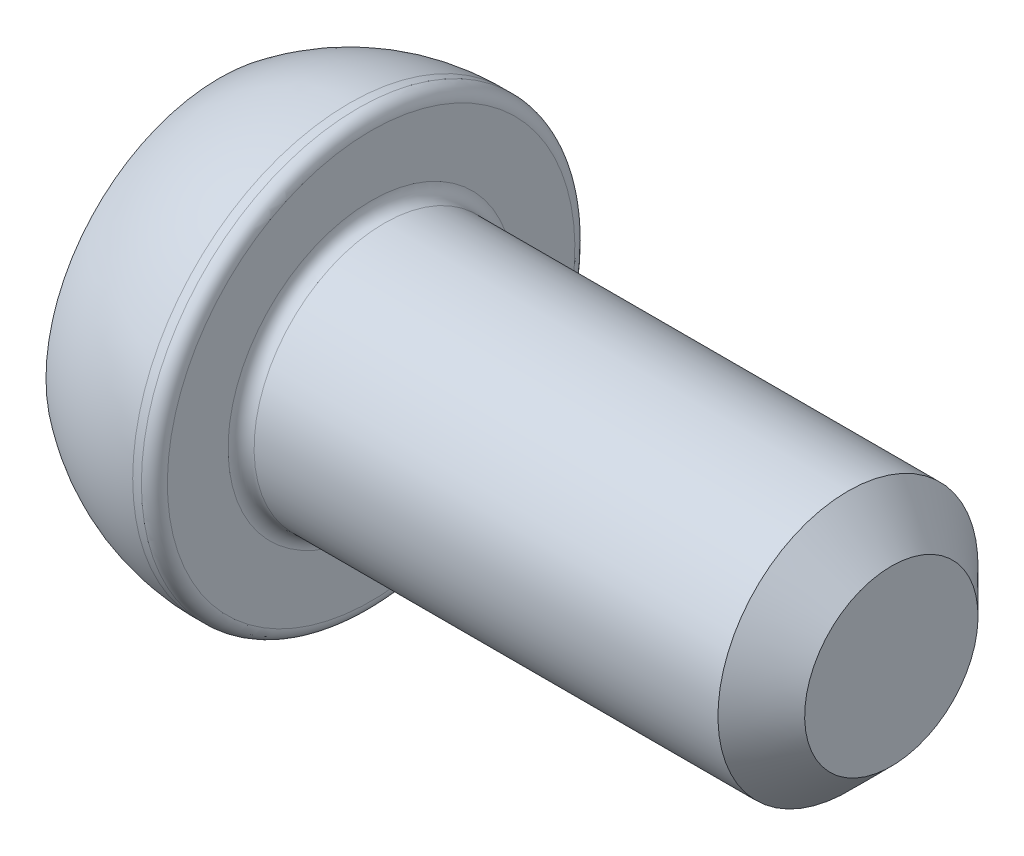
SolidWorks part; units mm, degrees
ref_plane "Спереди" through (0, 0, 0) normal (0, 0, 1) x (1, 0, 0)
ref_plane "Сверху" through (0, 0, 0) normal (0, 1, 0) x (1, 0, 0)
ref_plane "Справа" through (0, 0, 0) normal (1, 0, 0) x (0, 0, -1)
sketch "Эскиз1" plane through (0, 0, 0) normal (0, 0, 1) x (1, 0, 0)
  line L0 (0, 0) -> (0, 4)
  line L1 (3, 5) -> (3.5, 5)
  line L2 (3.5, 5) -> (3.5, 3)
  line L3 (3.5, 3) -> (15.5, 3)
  line L4 (15.5, 3) -> (15.5, 0)
  line L5 (15.5, 0) -> (0, 0) construction
  line L6 (0, 0) -> (15.5, 0)
  arc A0 (0, 4) -> (3, 5) centre (3, 0) cw
  point P9 (3.5, 4)
  dimension "D1" = 0.5
  dimension "D2" = 6
  dimension "D3" = 10
  dimension "D5" = 3.5
  dimension "D6" = 12
revolve "Повернуть1" add sketch "Эскиз1" angle 360 about L5
cosmetic thread "Условное изображение резьбы1" parameters "D2"=4.891
sketch "Эскиз2" plane through (0, 0, 0) normal (-1, 0, 0) x (0, 0, 1)
  line L1 (1.1547, 2) -> (-1.1547, 2)
  line L2 (-1.1547, 2) -> (-2.3094, 0)
  line L3 (-2.3094, 0) -> (-1.1547, -2)
  line L4 (-1.1547, -2) -> (1.1547, -2)
  line L5 (1.1547, -2) -> (2.3094, 0)
  line L6 (2.3094, 0) -> (1.1547, 2)
  circle A0 centre (0, 0) radius 2 construction
  dimension "D1" = 4
extrude "Вырез-Вытянуть1" cut sketch "Эскиз2" against normal blind 2
fillet "Скругление1" radius 0.3 2 edges at (3.5, 3, 0) (3.5, 5, 0)
chamfer "Фаска1" distance 1 angle 45 1 edges at (15.5, 3, 0)
